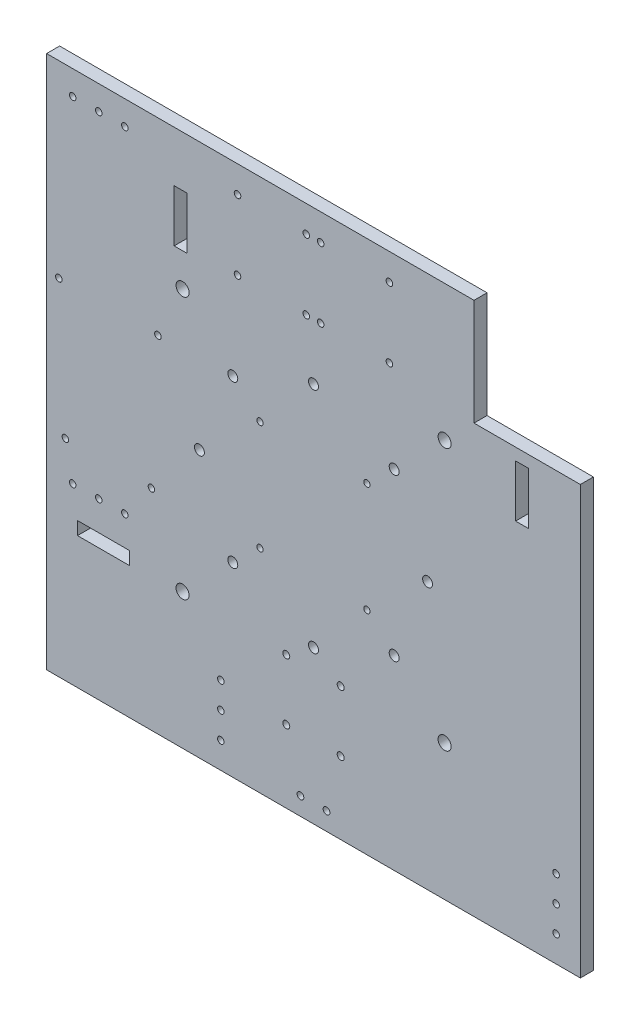
SolidWorks part; units mm, degrees
material "Perspex (TM) GS Acrylic Cast Sheet"
ref_plane "Front Plane" through (0, 0, 0) normal (0, 0, 1) x (1, 0, 0)
ref_plane "Top Plane" through (0, 0, 0) normal (0, 1, 0) x (1, 0, 0)
ref_plane "Right Plane" through (0, 0, 0) normal (1, 0, 0) x (0, 0, -1)
sketch "Sketch1" plane through (0, 0, 0) normal (0, 0, 1) x (1, 0, 0)
  line L0 (-130, 130) -> (130, 130)
  line L1 (130, 130) -> (130, -130)
  line L2 (130, -130) -> (-130, -130)
  line L3 (-130, -130) -> (-130, 130)
  line L4 (-127.2111, 46.4948) -> (-127.2111, -20.8155)
  line L5 (-29, 8) -> (-29, -8)
  line L6 (-29, 8) -> (-26.035, 8)
  line L7 (-26.035, 8) -> (-26.035, -8)
  line L8 (32.385, 33.02) -> (-32.385, 33.02)
  line L9 (-26.035, -8) -> (-29, -8)
  line L10 (-32.385, 33.02) -> (-32.385, -33.02)
  line L11 (-32.385, -33.02) -> (32.385, -33.02)
  line L12 (32.385, -33.02) -> (32.385, 33.02)
  line L13 (-114.5093, -33.5173) -> (-85.1363, -33.5173)
  line L14 (-120.8611, 52.8448) -> (-78.787, 52.8448)
  line L15 (-86.6259, 52.8448) -> (-86.6259, 35.8342)
  line L16 (-72.437, -20.8179) -> (-72.437, 46.4948)
  line L17 (-86.6259, 35.8342) -> (-102.1085, 35.8342)
  line L18 (-40, 120) -> (40, 120)
  line L19 (-102.1085, 35.8342) -> (-102.1085, 52.8448)
  line L31 (-40, 120) -> (-40, 80)
  line L32 (-40, 80) -> (40, 80)
  line L33 (40, 80) -> (40, 120)
  line L34 (-35, 100) -> (-35, 114.5)
  line L35 (-35, 114.5) -> (-29, 114.5)
  line L36 (-29, 114.5) -> (-29, 85.5)
  line L37 (-29, 85.5) -> (-35, 85.5)
  line L38 (-35, 85.5) -> (-35, 100)
  line L46 (16.75, -63) -> (16.75, -97)
  line L49 (16.75, -97) -> (-16.75, -97)
  line L50 (-16.75, -97) -> (-16.75, -63)
  line L51 (-16.75, -63) -> (16.75, -63)
  line L56 (120, 41.2) -> (120, -41.2)
  line L57 (45, 41.2) -> (45, -41.2)
  line L58 (120, 41.2) -> (45, 41.2)
  line L60 (45, -41.2) -> (120, -41.2)
  circle A0 centre (-26.035, 26.67) radius 1.55
  circle A1 centre (-26.035, -26.67) radius 1.55
  circle A2 centre (26.035, 26.67) radius 1.55
  circle A3 centre (26.035, -26.67) radius 1.55
  circle A4 centre (-124.0361, 38.2377) radius 1.5875
  circle A5 centre (-120.8611, -27.8002) radius 1.5875
  arc A6 (-127.2111, -20.8155) -> (-114.5093, -33.5173) centre (-114.5093, -20.8155) ccw
  arc A7 (-85.1363, -33.5173) -> (-72.437, -20.8179) centre (-85.1363, -20.8179) ccw
  arc A8 (-120.8611, 52.8448) -> (-127.2111, 46.4948) centre (-120.8611, 46.4948) ccw
  arc A9 (-72.437, 46.4948) -> (-78.787, 52.8448) centre (-78.787, 46.4948) ccw
  circle A10 centre (-75.7761, 38.2398) radius 1.5875
  circle A11 centre (-37, 117) radius 1.6
  circle A12 centre (-37, 83) radius 1.6
  circle A13 centre (-3.5, 117) radius 1.6
  circle A14 centre (-3.5, 83) radius 1.6
  circle A15 centre (3.5, 117) radius 1.6
  circle A16 centre (37, 117) radius 1.6
  circle A17 centre (37, 83) radius 1.6
  circle A18 centre (3.5, 83) radius 1.6
  circle A19 centre (-13.25, -65.25) radius 1.7
  circle A20 centre (13.25, -65.25) radius 1.7
  circle A21 centre (13.25, -94.75) radius 1.7
  circle A22 centre (-13.25, -94.75) radius 1.7
  circle A23 centre (-76.1972, 90.422) radius 3.175
  circle A24 centre (0, 55.575) radius 2.415
  circle A25 centre (-55.575, 0) radius 2.415
  circle A26 centre (0, -55.575) radius 2.415
  circle A27 centre (55.575, 0) radius 2.415
  circle A28 centre (-39.2975, 39.2975) radius 2.415
  circle A29 centre (39.2975, 39.2975) radius 2.415
  circle A30 centre (39.2975, -39.2975) radius 2.415
  circle A31 centre (-39.2975, -39.2975) radius 2.415
  circle A32 centre (76.33, 76.33) radius 3.175
  circle A33 centre (76.33, -76.33) radius 3.175
  circle A34 centre (-76.33, -76.33) radius 3.175
  arc A35 (-2.4144, 55.5225) -> (-37.5531, 40.9676) centre (0, 0) ccw
  arc A36 (37.5531, 40.9676) -> (2.4144, 55.5225) centre (0, 0) ccw
  arc A37 (55.5225, 2.4144) -> (40.9676, 37.5531) centre (0, 0) ccw
  arc A38 (40.9676, -37.5531) -> (55.5225, -2.4144) centre (0, 0) ccw
  arc A39 (2.4144, -55.5225) -> (37.5531, -40.9676) centre (0, 0) ccw
  arc A40 (-37.5531, -40.9676) -> (-2.4144, -55.5225) centre (0, 0) ccw
  arc A41 (-55.5225, -2.4144) -> (-40.9676, -37.5531) centre (0, 0) ccw
  arc A42 (-40.9676, 37.5531) -> (-55.5225, 2.4144) centre (0, 0) ccw
  circle A43 centre (-78.9511, -27.8002) radius 1.5875
  circle A44 centre (6.35, -121.3) radius 1.651
  circle A45 centre (-6.35, -121.3) radius 1.651
  circle A46 centre (121.3, 126.35) radius 1.651
  circle A47 centre (121.3, 113.65) radius 1.651
  point P127 (127.65, 120)
  point P128 (-120, -120)
  point P129 (0, -127.65)
extrude "Boss-Extrude2" add sketch "Sketch1" along normal blind 6.35 contours L0 L1 L2 L3 | A10 | A43 | A5 | A4 | A25 | A28 | A24 | A31 | A26 | A30 | A27 | A29 | A1 | A3 | A2 | A0 | A22 | A21 | A20 | A19 | A45 | A44 | A46 | A47 | A17 | A16 | A18 | A14 | A15 | A13 | A11 | A12
sketch "Sketch2" plane through (0, 0, 0) normal (0, 0, -1) x (-1, 0, 0)
  circle A0 centre (0, 0) radius 55.6086 construction
sketch "Sketch5" plane through (0, 0, 0) normal (0, 0, -1) x (-1, 0, 0)
  line L0 (-78.2, 78.2) -> (-78.2, 131)
  line L1 (-78.2, 131) -> (-131, 131)
  line L2 (-131, 131) -> (-131, 78.2)
  line L3 (-131, 78.2) -> (-78.2, 78.2)
  line L4 (-130, 130) -> (-130, 79.2)
  line L5 (-130, 79.2) -> (-79.2, 79.2)
  line L6 (-79.2, 79.2) -> (-79.2, 130)
  line L7 (-79.2, 130) -> (-130, 130)
  line L8 (-130, 130) -> (-130, 79.2)
  line L9 (-130, 79.2) -> (-79.2, 79.2)
  line L10 (-79.2, 79.2) -> (-79.2, 130)
  line L11 (-79.2, 130) -> (-130, 130)
  dimension "D1" = 0
  dimension "D2" = 1
extrude "Cut-Extrude1" cut sketch "Sketch5" against normal through all contours L2 L3 L0 L1
sketch "Sketch6" plane through (0, 0, 0) normal (0, 0, -1) x (-1, 0, 0)
  circle A0 centre (63.7786, 63.7786) radius 3.175 construction
  circle A1 centre (-63.8746, 63.7786) radius 3.175 construction
  circle A2 centre (-63.8746, -63.8746) radius 3.175 construction
  circle A3 centre (63.7786, -63.8746) radius 3.175 construction
  circle A4 centre (63.7786, 63.7786) radius 3.175
  circle A5 centre (-63.8746, 63.7786) radius 3.175
  circle A6 centre (-63.8746, -63.8746) radius 3.175
  circle A7 centre (63.7786, -63.8746) radius 3.175
extrude "Cut-Extrude2" cut sketch "Sketch6" against normal through all contours A7 | A6 | A5 | A4
sketch "Sketch7" plane through (0, 0, 0) normal (0, 0, -1) x (-1, 0, 0)
  circle A0 centre (91.9, 118.189) radius 1.5875 construction
  circle A1 centre (104.6, 118.189) radius 1.5875 construction
  circle A2 centre (117.3, 118.189) radius 1.5875 construction
  circle A3 centre (91.9, -45.133) radius 1.5875 construction
  circle A4 centre (104.6, -45.133) radius 1.5875 construction
  circle A5 centre (117.3, -45.133) radius 1.5875 construction
  circle A6 centre (45.133, -117.3) radius 1.5875 construction
  circle A7 centre (45.133, -104.6) radius 1.5875 construction
  circle A8 centre (45.133, -91.9) radius 1.5875 construction
  circle A9 centre (-118.189, -117.3) radius 1.5875 construction
  circle A10 centre (-118.189, -104.6) radius 1.5875 construction
  circle A11 centre (-118.189, -91.9) radius 1.5875 construction
  circle A12 centre (91.9, 118.189) radius 1.5875
  circle A13 centre (104.6, 118.189) radius 1.5875
  circle A14 centre (117.3, 118.189) radius 1.5875
  circle A15 centre (91.9, -45.133) radius 1.5875
  circle A16 centre (104.6, -45.133) radius 1.5875
  circle A17 centre (117.3, -45.133) radius 1.5875
  circle A18 centre (45.133, -117.3) radius 1.5875
  circle A19 centre (45.133, -104.6) radius 1.5875
  circle A20 centre (45.133, -91.9) radius 1.5875
  circle A21 centre (-118.189, -117.3) radius 1.5875
  circle A22 centre (-118.189, -104.6) radius 1.5875
  circle A23 centre (-118.189, -91.9) radius 1.5875
extrude "Cut-Extrude3" cut sketch "Sketch7" against normal through all
sketch "Sketch8" plane through (0, 0, 6.35) normal (0, 0, 1) x (1, 0, 0)
  line L1 (-114.9411, -59.4888) -> (-89.5411, -59.4888)
  line L2 (-114.9411, -59.4888) -> (-114.9411, -65.8388)
  line L3 (-114.9411, -65.8388) -> (-89.5411, -65.8388)
  line L4 (-89.5411, -59.4888) -> (-89.5411, -65.8388)
  line L5 (-67.8687, 105.3103) -> (-61.5187, 105.3103)
  line L6 (-67.8687, 105.3103) -> (-67.8687, 79.9103)
  line L7 (-67.8687, 79.9103) -> (-61.5187, 79.9103)
  line L8 (-61.5187, 105.3103) -> (-61.5187, 79.9103)
  line L10 (98.4543, 72.381) -> (104.8043, 72.381)
  line L11 (98.4543, 72.381) -> (98.4543, 46.981)
  line L12 (98.4543, 46.981) -> (104.8043, 46.981)
  line L13 (104.8043, 72.381) -> (104.8043, 46.981)
  dimension "D1" = 25.4
  dimension "D2" = 6.35
  dimension "D3" = 25.4
  dimension "D4" = 6.35
  dimension "D5" = 25.4
  dimension "D6" = 6.35
extrude "Cut-Extrude4" cut sketch "Sketch8" against normal through all
